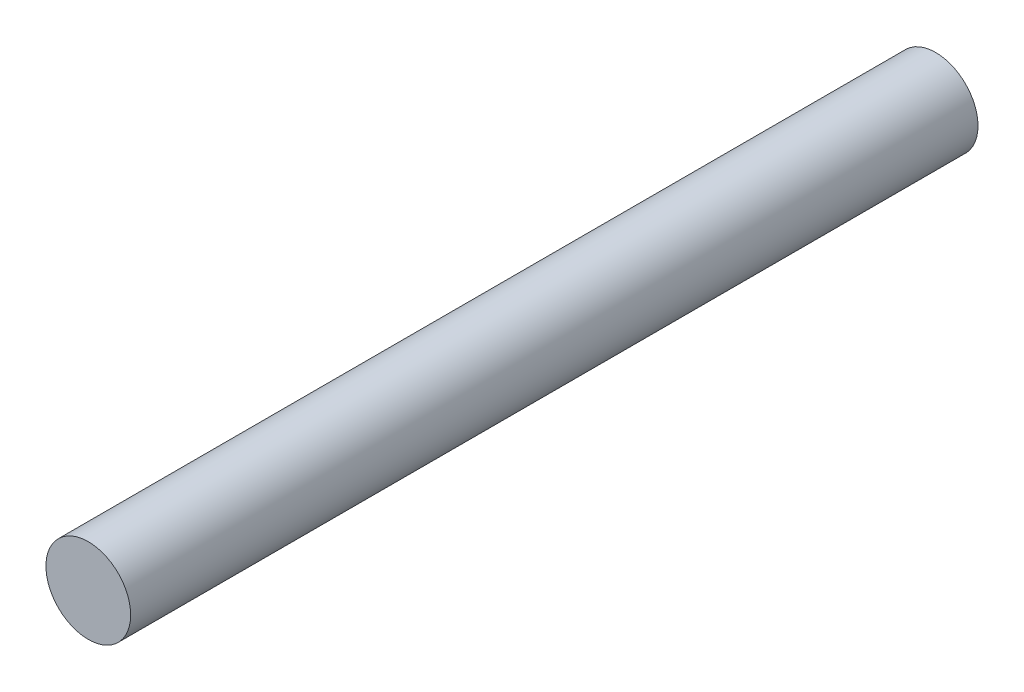
SolidWorks part; units mm, degrees
ref_plane "Front Plane" through (0, 0, 0) normal (0, 0, 1) x (1, 0, 0)
ref_plane "Top Plane" through (0, 0, 0) normal (0, 1, 0) x (1, 0, 0)
ref_plane "Right Plane" through (0, 0, 0) normal (1, 0, 0) x (0, 0, -1)
sketch "Sketch1" plane through (0, 0, 0) normal (0, 0, 1) x (1, 0, 0)
  circle A0 centre (0, 0) radius 0.15
extrude "Boss-Extrude1" add sketch "Sketch1" along normal blind 3
